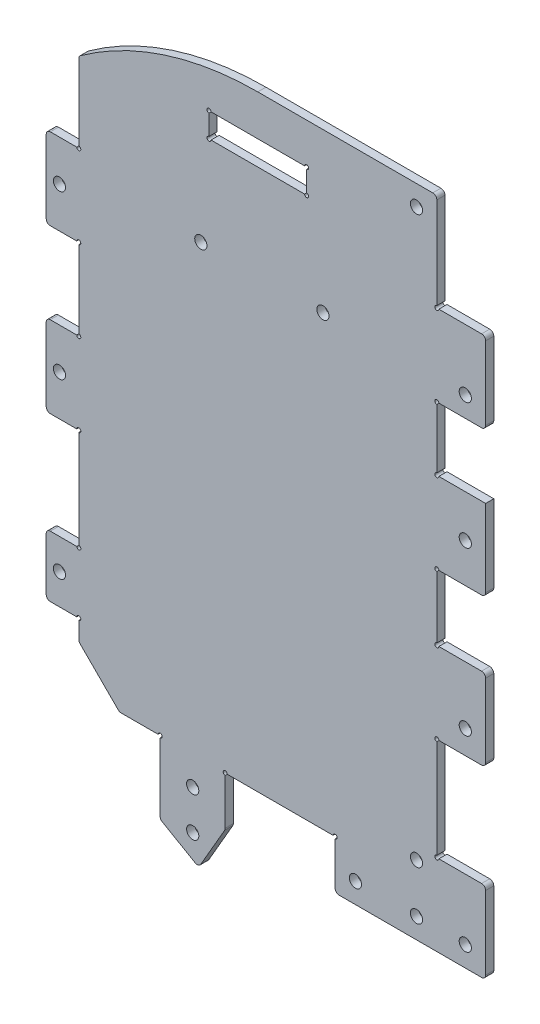
SolidWorks part; units mm, degrees
material "环氧板3240"
ref_plane "前视基准面" through (0, 0, 0) normal (0, 0, 1) x (1, 0, 0)
ref_plane "上视基准面" through (0, 0, 0) normal (0, 1, 0) x (1, 0, 0)
ref_plane "右视基准面" through (0, 0, 0) normal (1, 0, 0) x (0, 0, -1)
other "Configuration Table"
sketch "草图1" plane through (0, 0, 0) normal (0, 0, 1) x (1, 0, 0)
  line L0 (0, 60.1186) -> (-44, 60.1186) construction
  line L1 (44, -74.5) -> (-44, -74.5)
  line L2 (44, -74.5) -> (44, 60.1186)
  line L4 (-44, -74.5) -> (-44, 60.1186)
  line L5 (52, -5.1) -> (52, -21.3) construction
  line L6 (52, 30.5) -> (52, 14.9) construction
  line L7 (-24, -74.5) -> (-24, -92.3247)
  line L8 (0, -74.5) -> (0, 74.5) construction
  line L9 (-8, -86.5) -> (-8, -74.5)
  line L10 (56, -66.5) -> (56, -86.5)
  line L11 (-24, -86.5512) -> (-12.0222, -93.4666) construction
  line L12 (56, -86.5) -> (19, -86.5)
  line L13 (0, 74.5) -> (0, 60.1186) construction
  line L14 (19, -86.5) -> (19, -74.5)
  line L15 (-44, -64.5) -> (-34, -74.5)
  line L16 (-44, -81.5) -> (56, -81.5) construction
  line L17 (44, -74.5) -> (44, -86.5) construction
  line L18 (0, 60.1186) -> (-44, 60.1186) construction
  line L19 (-52, -44.5) -> (-52, -59.5)
  line L20 (-52, -59.5) -> (-44, -59.5)
  line L21 (-52, -44.5) -> (-44, -44.5)
  line L22 (46, -21.3) -> (56, -21.3)
  line L25 (44, -5.1) -> (52, -5.1)
  line L26 (52, -5.1) -> (52, 14.9) construction
  line L27 (52, 14.9) -> (44, 14.9)
  line L28 (44, -41.3) -> (52, -41.3)
  line L29 (52, -41.3) -> (52, -21.3) construction
  line L30 (52, -21.3) -> (44, -21.3)
  line L31 (44, 30.5) -> (52, 30.5)
  line L32 (52, 30.5) -> (52, 50.5) construction
  line L33 (52, 50.5) -> (44, 50.5)
  line L34 (-44, -19.5) -> (-52, -19.5)
  line L35 (-52, -19.5) -> (-52, 0.5)
  line L36 (-52, 0.5) -> (-44, 0.5)
  line L37 (-52, 40.5) -> (-44, 40.5)
  line L38 (-52, 20.5) -> (-52, 40.5)
  line L39 (-44, 20.5) -> (-52, 20.5)
  line L40 (0, 74.5) -> (44, 74.5)
  line L41 (46, -21.3) -> (46, -41.3) construction
  line L42 (44, 74.5) -> (44, 60.1186)
  line L43 (0, 60.1186) -> (44, 60.1186) construction
  line L48 (46, -41.3) -> (56, -41.3)
  line L49 (56, -21.3) -> (56, -41.3)
  line L50 (46, -21.3) -> (56, -41.3) construction
  line L51 (46, -41.3) -> (56, -21.3) construction
  line L52 (51, 40.5) -> (51, 30.5) construction
  line L53 (46, 14.9) -> (56, 14.9)
  line L54 (46, 14.9) -> (46, -5.1) construction
  line L55 (46, -5.1) -> (56, -5.1)
  line L56 (56, 14.9) -> (56, -5.1)
  line L57 (46, 14.9) -> (56, -5.1) construction
  line L58 (46, -5.1) -> (56, 14.9) construction
  line L59 (46, 50.5) -> (56, 50.5)
  line L60 (46, 50.5) -> (46, 30.5) construction
  line L61 (46, 30.5) -> (56, 30.5)
  line L62 (56, 50.5) -> (56, 30.5)
  line L63 (46, 50.5) -> (56, 30.5) construction
  line L64 (46, 30.5) -> (56, 50.5) construction
  line L65 (44, -66.5) -> (56, -66.5)
  line L66 (51, 35.5) -> (-44, 35.5) construction
  line L67 (51, 4.9) -> (51, -5.1) construction
  line L69 (51, -31.3) -> (51, -41.3) construction
  line L70 (-24, -92.3247) -> (-14.5222, -97.7967)
  line L71 (-14.5222, -97.7967) -> (-8, -86.5)
  circle A1 centre (39, -69.5) radius 1.5
  circle A3 centre (39, 69.5) radius 1.5
  circle A5 centre (51, 35.5) radius 1.5
  circle A9 centre (51, -81.5) radius 1.5
  circle A10 centre (24, -81.5) radius 1.5
  circle A11 centre (39, -81.5) radius 1.5
  circle A13 centre (0, 0) radius 74.5 construction
  arc A14 (0, 74.5) -> (-44, 60.1186) centre (0, 0) ccw
  circle A15 centre (-16, -81.5) radius 1.5
  circle A16 centre (-14, 35.5) radius 1.5
  circle A17 centre (16, 35.5) radius 1.5
  circle A19 centre (51, -35.5) radius 1.5
  circle A20 centre (51, 4.5) radius 1.5
  circle A21 centre (-16, -91.17) radius 1.5
  point P10 (0, 0)
  point P35 (51, -31.3)
  point P70 (51, 4.9)
  point P72 (51, 40.5)
  dimension "D4" = 149
  dimension "D13" = 3
  dimension "D25" = 3
  dimension "D29" = 5
  dimension "D30" = 25
  dimension "D31" = 20
  dimension "D10" = 3
  dimension "D11" = 5
  dimension "D26" = 5
  dimension "D27" = 15
  dimension "D28" = 40
  dimension "D35" = 35
  dimension "D36" = 30
  dimension "D32" = 8
  dimension "D38" = 3
  dimension "D39" = 0.4
  dimension "D40" = 14.2
  dimension "D43" = 3
  dimension "D46" = 8
  dimension "D48" = 9.67
  dimension "D50" = 0
  dimension "D1" = 88
  dimension "D2" = 5
  dimension "D5" = 5
  dimension "D6" = 12
  dimension "D7" = 30
  dimension "D8" = 24
  dimension "D9" = 5
  dimension "D12" = 15.6
  dimension "D14" = 8
  dimension "D16" = 5
  dimension "D17" = 20
  dimension "D18" = 5
  dimension "D19" = 5
  dimension "D20" = 20
  dimension "D22" = 16.2
  dimension "D23" = 10
  dimension "D24" = 2
  dimension "D33" = 10
  dimension "D34" = 45
  dimension "D37" = 20
  dimension "D41" = 20
  dimension "D42" = 8
  dimension "D44" = 5
  dimension "D45" = 15
  dimension "D47" = 12
  dimension "D49" = 5
extrude "凸台-拉伸2" add sketch "草图1" along normal blind 2
sketch "草图2" plane through (0, 0, 0) normal (0, 0, -1) x (-1, 0, 0)
  line L0 (48.75, 40.5) -> (48.75, -59.5) construction
  line L2 (46, 30.5) -> (46, -9.5) construction
  line L4 (52, 0.5) -> (44, 0.5) construction
  line L5 (52, -44.5) -> (44, -44.5) construction
  line L6 (52, -59.5) -> (44, -59.5) construction
  line L7 (52, 40.5) -> (44, 40.5) construction
  line L8 (44, 0.5) -> (44, 20.5) construction
  circle A0 centre (48.75, 30.5) radius 1.5
  circle A1 centre (48.75, 30.5) radius 2.75 construction
  circle A2 centre (48.75, -9.5) radius 1.5
  circle A3 centre (48.75, -52) radius 1.5
  dimension "D1" = 3
  dimension "D2" = 5.5
  dimension "D4" = 10
  dimension "D5" = 10
  dimension "D6" = 7.5
  dimension "D3" = 2
extrude "切除-拉伸1" cut sketch "草图2" against normal blind 10
sketch "草图3" plane through (0, 0, 0) normal (0, 0, -1) x (-1, 0, 0)
  line L0 (0, 0) -> (0, -81.5223) construction
  line L1 (52, 40.5) -> (44, 40.5) construction
  circle A0 centre (-44, 50.5) radius 0.5
  circle A1 centre (-44, 30.5) radius 0.5
  circle A2 centre (-44, 14.9) radius 0.5
  circle A3 centre (-44, -5.1) radius 0.5
  circle A4 centre (-44, -21.3) radius 0.5
  circle A5 centre (-44, -41.3) radius 0.5
  circle A6 centre (-44, -66.5) radius 0.5
  circle A10 centre (44, 40.5) radius 0.5
  circle A11 centre (44, 20.5) radius 0.5
  circle A12 centre (44, 0.5) radius 0.5
  circle A13 centre (44, -19.5) radius 0.5
  circle A14 centre (44, -44.5) radius 0.5
  circle A15 centre (44, -59.5) radius 0.5
  circle A16 centre (-19, -74.5) radius 0.5
  circle A17 centre (8, -74.5) radius 0.5
  circle A18 centre (24, -74.5) radius 0.5
  dimension "D1" = 1
extrude "切除-拉伸2" cut sketch "草图3" against normal through all
fillet "圆角1" radius 1 21 edges at (-52, -44.5, 1) (-52, 0.5, 1) (-52, 40.5, 1) (-44, 60.1186, 1) (44, 74.5, 1) (56, 50.5, 1) (-52, 20.5, 1) (-52, -19.5, 1) (-52, -59.5, 1) (19, -86.5, 1) (56, -86.5, 1) (56, -66.5, 1) (56, -21.3, 1) (56, -41.3, 1) (56, -5.1, 1) (56, 30.5, 1) (-44, -64.5, 1) (-34, -74.5, 1) (-24, -92.3247, 1) (-8, -86.5, 1) (-14.5222, -97.7967, 1)
sketch "草图4" plane through (0, 0, 0) normal (0, 0, -1) x (-1, 0, 0)
  line L1 (-12, 64.5) -> (12, 64.5)
  line L2 (-12, 64.5) -> (-12, 58.5)
  line L3 (-12, 58.5) -> (12, 58.5)
  line L4 (12, 64.5) -> (12, 58.5)
  line L5 (-19, -74.5) -> (8, -74.5) construction
  line L7 (-44, 51) -> (44, 51) construction
  line L8 (44, 41) -> (44, 59.6091) construction
  line L9 (0, 51) -> (0, 74.5) construction
  circle A0 centre (-12, 64.5) radius 0.5
  circle A1 centre (-12, 58.5) radius 0.5
  circle A2 centre (12, 64.5) radius 0.5
  circle A3 centre (12, 58.5) radius 0.5
  dimension "D4" = 1
  dimension "D1" = 24
  dimension "D2" = 6
  dimension "D3" = 133
extrude "切除-拉伸3" cut sketch "草图4" against normal through all contours L1 A0 L2 | L2 A1 L3 | A3 L4 A2 L1 A0 L2 A1 L3 | L4 A2 L1 | L3 A3 L4 | L4 A3 L3 | L1 A2 L4 | L2 A0 L1 | L3 A1 L2
